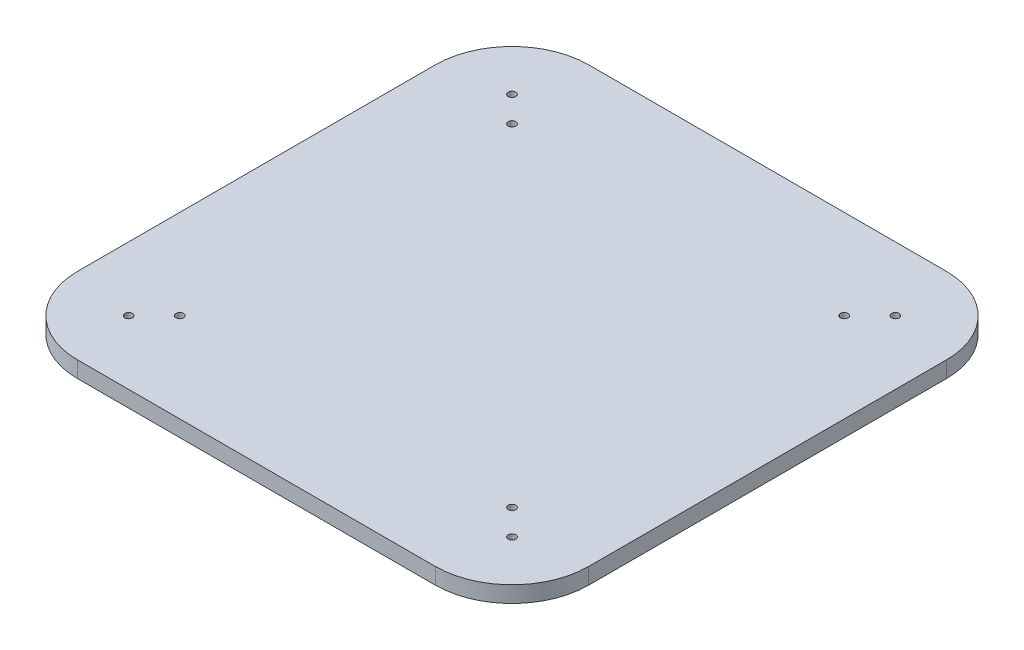
SolidWorks part; units mm, degrees
ref_plane "Front Plane" through (0, 0, 0) normal (0, 0, 1) x (1, 0, 0)
ref_plane "Top Plane" through (0, 0, 0) normal (0, 1, 0) x (1, 0, 0)
ref_plane "Right Plane" through (0, 0, 0) normal (1, 0, 0) x (0, 0, -1)
sketch "Sketch1" plane through (0, 0, 0) normal (0, 1, 0) x (1, 0, 0)
  line L0 (0, 113.0841) -> (0, -92.9907) construction
  line L1 (-70, -100) -> (70, -100)
  line L2 (-152.8037, 0) -> (116.8224, 0) construction
  line L3 (-100, 70) -> (-100, -70)
  line L4 (-70, 100) -> (70, 100)
  line L5 (100, 70) -> (100, -70)
  line L6 (-70, -70) -> (70, 70) construction
  arc A0 (100, 70) -> (70, 100) centre (70, 70) ccw
  arc A1 (100, -70) -> (70, -100) centre (70, -70) cw
  arc A2 (-100, -70) -> (-70, -100) centre (-70, -70) ccw
  arc A3 (-100, 70) -> (-70, 100) centre (-70, 70) cw
  circle A4 centre (75, 75) radius 1.5
  circle A5 centre (65, 65) radius 1.5
  circle A6 centre (65, -65) radius 1.5
  circle A7 centre (75, -75) radius 1.5
  circle A8 centre (-65, -65) radius 1.5
  circle A9 centre (-75, -75) radius 1.5
  circle A10 centre (-65, 65) radius 1.5
  circle A11 centre (-75, 75) radius 1.5
  point P10 (100, 100)
  point P12 (100, 0)
  point P18 (0, -100)
  point P21 (0, 100)
  point P42 (0, 0)
  dimension "D3" = 30
  dimension "D4" = 65
  dimension "D1" = 100
  dimension "D2" = 100
  dimension "D5" = 75
  dimension "D6" = 4
extrude "Boss-Extrude1" add sketch "Sketch1" along normal blind 6.35
